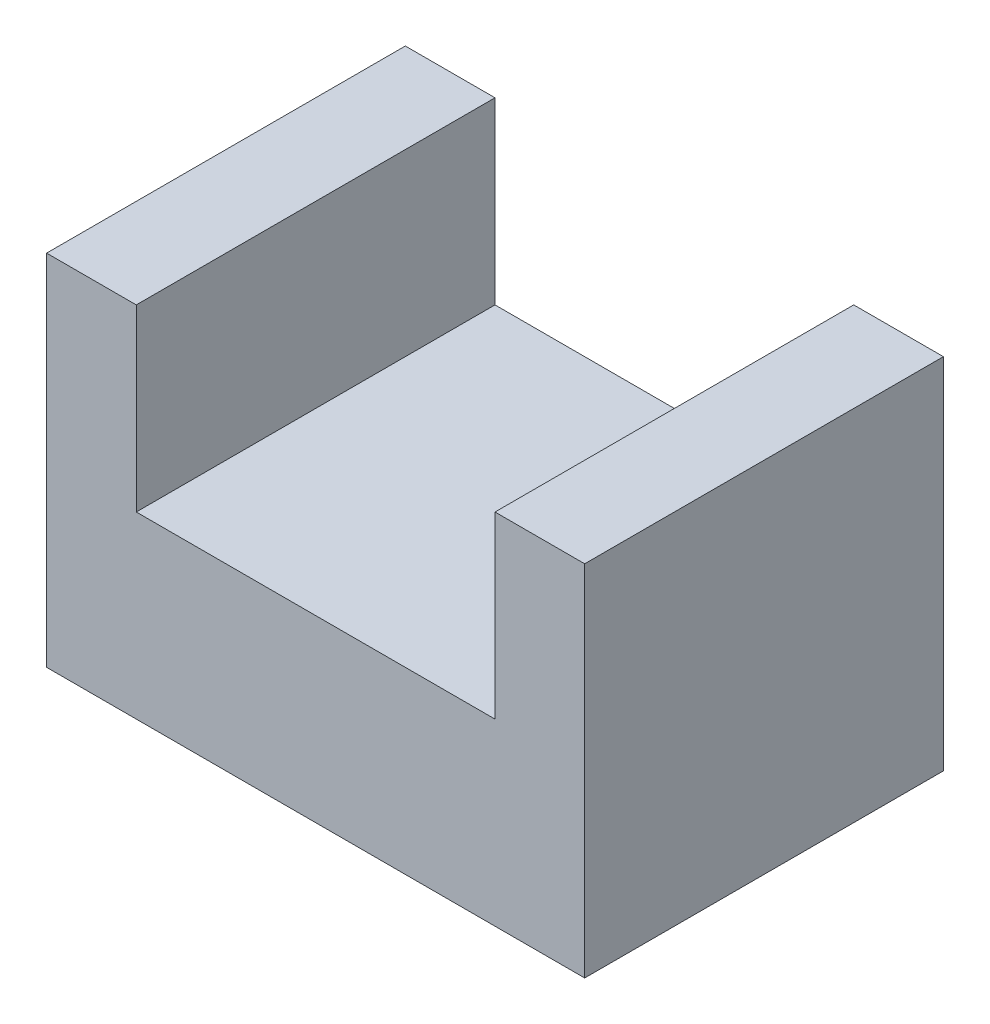
SolidWorks part; units mm, degrees
ref_plane "Front" through (0, 0, 0) normal (0, 0, 1) x (1, 0, 0)
ref_plane "Top" through (0, 0, 0) normal (0, 1, 0) x (1, 0, 0)
ref_plane "Right" through (0, 0, 0) normal (1, 0, 0) x (0, 0, -1)
sketch "Sketch2" plane through (0, 0, 0) normal (0, 0, 1) x (1, 0, 0)
  line L0 (-36.6151, 37.0449) -> (-36.6151, -13.7551)
  line L1 (-36.6151, -13.7551) -> (39.5849, -13.7551)
  line L2 (39.5849, -13.7551) -> (39.5849, 37.0449)
  line L3 (39.5849, 37.0449) -> (26.8849, 37.0449)
  line L4 (26.8849, 37.0449) -> (26.8849, 11.6449)
  line L5 (26.8849, 11.6449) -> (-23.9151, 11.6449)
  line L6 (-23.9151, 11.6449) -> (-23.9151, 37.0449)
  line L7 (-23.9151, 37.0449) -> (-36.6151, 37.0449)
  dimension "D1" = 50.8
  dimension "D2" = 76.2
  dimension "D3" = 12.7
  dimension "D4" = 12.7
  dimension "D5" = 25.4
  dimension "D6" = 25.4
extrude "Boss-Extrude1" add sketch "Sketch2" along normal blind 50.8
